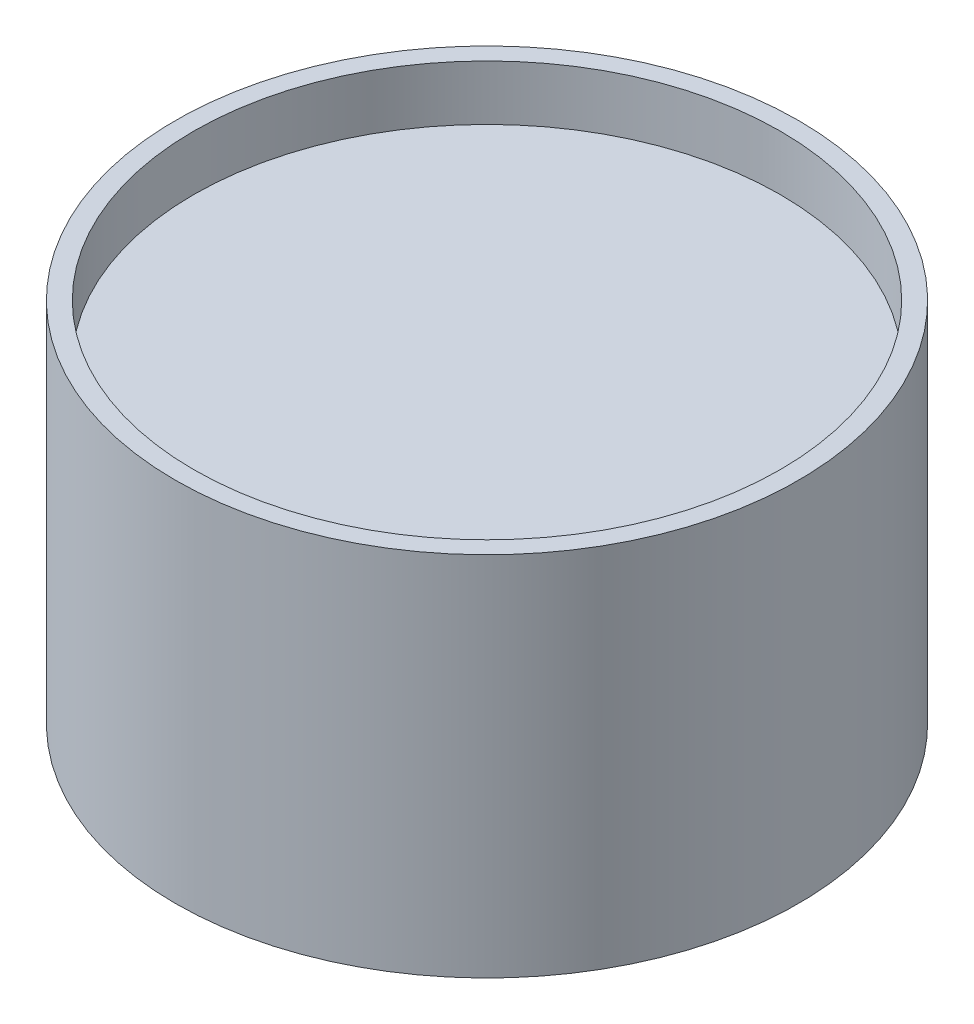
SolidWorks part; units mm, degrees
ref_plane "Front Plane" through (0, 0, 0) normal (0, 0, 1) x (1, 0, 0)
ref_plane "Top Plane" through (0, 0, 0) normal (0, 1, 0) x (1, 0, 0)
ref_plane "Right Plane" through (0, 0, 0) normal (1, 0, 0) x (0, 0, -1)
sketch "Sketch1" plane through (0, 0, 0) normal (0, 1, 0) x (1, 0, 0)
  circle A0 centre (0, 0) radius 17
  dimension "D1" = 34
extrude "Boss-Extrude1" add sketch "Sketch1" along normal blind 20
sketch "Sketch2" plane through (0, 20, 0) normal (0, 1, 0) x (1, 0, 0)
  circle A0 centre (0, 0) radius 16
  dimension "D1" = 32
extrude "Cut-Extrude1" cut sketch "Sketch2" against normal blind 3
sketch "Sketch3" plane through (0, 0, 0) normal (0, -1, 0) x (1, 0, 0)
  circle A0 centre (0, 0) radius 1
  dimension "D1" = 2
extrude "Cut-Extrude2" cut sketch "Sketch3" against normal blind 2
fillet "Fillet1" radius 1 1 edges at (0, 2, -1)
